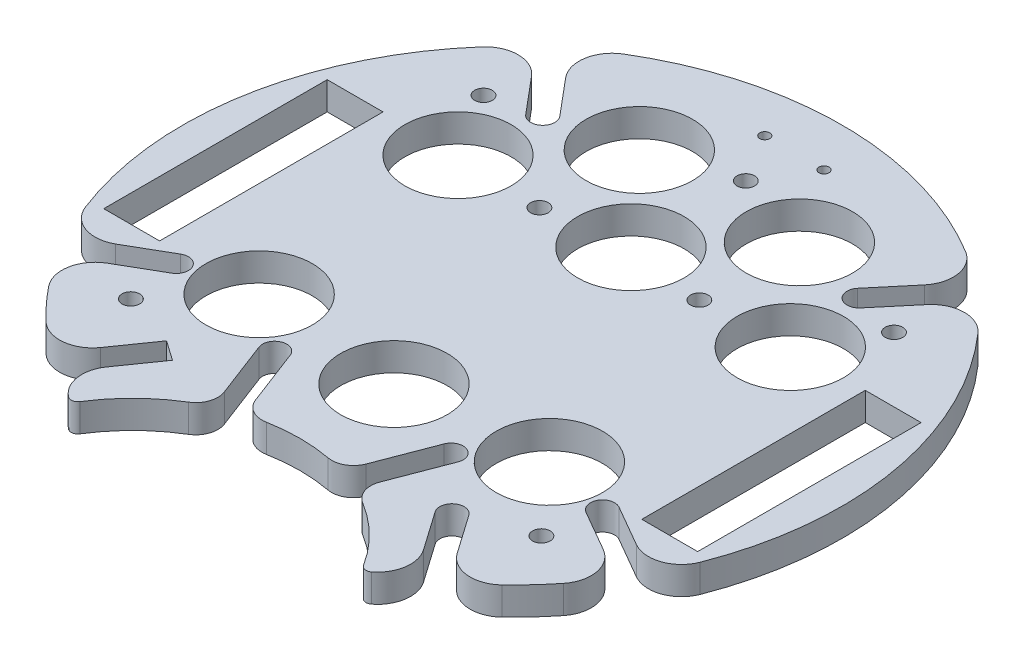
SolidWorks part; units mm, degrees
ref_plane "Front Plane" through (0, 0, 0) normal (0, 0, 1) x (1, 0, 0)
ref_plane "Top Plane" through (0, 0, 0) normal (0, 1, 0) x (1, 0, 0)
ref_plane "Right Plane" through (0, 0, 0) normal (1, 0, 0) x (0, 0, -1)
sketch "Sketch1" plane through (0, 0, 0) normal (0, 1, 0) x (1, 0, 0)
  line L0 (0, 0) -> (-32.9956, -67.352) construction
  line L1 (0, 86.2583) -> (0, -96.8543) construction
  line L2 (0, 0) -> (32.9956, -67.352) construction
  line L3 (-32.9956, -67.352) -> (0, -86.402) construction
  line L4 (32.9956, -67.352) -> (0, -86.402) construction
  line L5 (0, 0) -> (-13.6167, -50.8184) construction
  line L6 (0, 0) -> (-43.0182, -61.4364) construction
  line L7 (0, 0) -> (-48.2091, 57.4533) construction
  line L8 (-83.3992, 0) -> (107.0959, 0) construction
  line L9 (54.8141, -25.4) -> (54.8141, 25.4)
  line L10 (-67.5141, -25.4) -> (-54.8141, -25.4)
  line L11 (-67.5141, -25.4) -> (-67.5141, 25.4)
  line L12 (-67.5141, 25.4) -> (-54.8141, 25.4)
  line L13 (-54.8141, 25.4) -> (-54.8141, -25.4)
  line L14 (67.5141, 25.4) -> (54.8141, 25.4)
  line L15 (67.5141, -25.4) -> (67.5141, 25.4)
  line L16 (67.5141, -25.4) -> (54.8141, -25.4)
  line L17 (0, 0) -> (13.6167, -50.8184) construction
  line L18 (-64.9519, -37.5) -> (0, 0) construction
  line L19 (0, 0) -> (48.2091, 57.4533) construction
  line L20 (0, 0) -> (43.0182, -61.4364) construction
  line L21 (64.9519, -37.5) -> (0, 0) construction
  line L22 (-40.1627, -62.1527) -> (-39.9022, -61.7807)
  line L23 (-34.3581, -44.2739) -> (-40.5201, -53.0742)
  line L24 (44.9916, 49.3407) -> (38.0699, 41.0917)
  line L26 (-29.8527, -47.4286) -> (-36.0148, -56.2289)
  line L27 (-59.208, -31.0083) -> (-49.8282, -25.5929)
  line L30 (-44.668, -58.998) -> (-44.6824, -59.0187)
  line L31 (-56.458, -35.7715) -> (-47.0782, -30.356)
  line L32 (-40.7784, 52.876) -> (-33.8566, 44.627)
  line L34 (40.7784, 52.876) -> (33.8566, 44.627)
  line L35 (56.458, -35.7715) -> (47.0782, -30.356)
  line L36 (-44.9916, 49.3407) -> (-38.0699, 41.0917)
  line L37 (59.208, -31.0083) -> (49.8282, -25.5929)
  line L40 (34.3581, -44.2739) -> (40.5201, -53.0742)
  line L41 (29.8527, -47.4286) -> (36.0148, -56.2289)
  line L42 (-13.6167, -50.8184) -> (-2.8571, -46.701) construction
  line L43 (17.721, -47.7876) -> (22.6182, -34.9901)
  line L44 (-12.4041, -46.2927) -> (-17.4815, -33.0244)
  line L45 (-13.6167, -50.8184) -> (-17.7255, -40.0812) construction
  line L46 (-17.721, -47.7876) -> (-22.6182, -34.9901)
  line L49 (12.4041, -46.2927) -> (17.4815, -33.0244)
  line L50 (-34.3581, -44.2739) -> (-29.8527, -47.4286)
  line L51 (-49.8282, -25.5929) -> (-47.0782, -30.356)
  line L52 (-22.6182, -34.9901) -> (-17.4815, -33.0244)
  line L53 (17.4815, -33.0244) -> (22.6182, -34.9901)
  line L54 (34.3581, -44.2739) -> (29.8527, -47.4286)
  line L55 (49.8282, -25.5929) -> (47.0782, -30.356)
  line L56 (33.8566, 44.627) -> (38.0699, 41.0917)
  line L57 (-38.0699, 41.0917) -> (-33.8566, 44.627)
  arc A0 (-56.3744, 49.4664) -> (-69.893, -27.2023) centre (0, 0) ccw
  arc A1 (-19.7932, -53.8469) -> (-32.2407, -66.1006) centre (0, -86.402) ccw
  arc A2 (38.9256, 64.1077) -> (-38.9256, 64.1077) centre (0, 0) ccw
  arc A3 (56.3744, 49.4664) -> (44.9543, 49.2959) centre (50.737, 44.5198) ccw
  arc A4 (-56.3744, 49.4664) -> (-44.9543, 49.2959) centre (-50.737, 44.5198) cw
  arc A5 (-69.893, -27.2023) -> (-59.0997, -30.9458) centre (-62.9037, -24.4821) ccw
  arc A6 (-51.8486, -54.1915) -> (-40.5201, -53.0742) centre (-46.6637, -48.7724) ccw
  arc A7 (-38.9256, 64.1077) -> (-40.7407, 52.8315) centre (-35.033, 57.6969) ccw
  arc A8 (-58.5044, -46.928) -> (-56.3497, -35.7089) centre (-52.654, -42.2352) cw
  arc A9 (-34.4197, -66.4939) -> (-36.0148, -56.2289) centre (-29.8711, -60.5307) cw
  arc A10 (38.9256, 64.1077) -> (40.7407, 52.8315) centre (35.033, 57.6969) cw
  arc A11 (58.5044, -46.928) -> (56.3497, -35.7089) centre (52.654, -42.2352) ccw
  arc A12 (69.893, -27.2023) -> (59.0997, -30.9458) centre (62.9037, -24.4821) cw
  arc A13 (34.4197, -66.4939) -> (36.0148, -56.2289) centre (29.8711, -60.5307) ccw
  arc A14 (51.8486, -54.1915) -> (40.5201, -53.0742) centre (46.6637, -48.7724) cw
  arc A15 (-58.5044, -46.928) -> (-51.8486, -54.1915) centre (0, 0) ccw
  arc A16 (-33.1901, -67.2563) -> (-32.9956, -67.352) centre (0, 0) ccw
  arc A17 (51.8486, -54.1915) -> (58.5044, -46.928) centre (0, 0) ccw
  arc A18 (69.893, -27.2023) -> (56.3744, 49.4664) centre (0, 0) ccw
  arc A19 (-19.7932, -53.8469) -> (-17.721, -47.7876) centre (-22.3908, -49.5745) ccw
  arc A20 (-6.9964, -48.9499) -> (-12.5843, -45.8219) centre (-7.9145, -44.0349) cw
  arc A21 (19.7932, -53.8469) -> (17.721, -47.7876) centre (22.3908, -49.5745) cw
  arc A22 (6.9964, -48.9499) -> (12.5843, -45.8219) centre (7.9145, -44.0349) ccw
  arc A23 (6.9964, -48.9499) -> (-6.9964, -48.9499) centre (0, -86.402) ccw
  arc A24 (32.2407, -66.1006) -> (19.7932, -53.8469) centre (0, -86.402) ccw
  circle A25 centre (-18.179, 24.3106) radius 2
  circle A26 centre (-32.9956, -24.5929) radius 12.095
  circle A27 centre (32.9956, -24.5929) radius 12.095
  circle A28 centre (37.7724, 25.4) radius 12.095
  circle A29 centre (-37.7724, 25.4) radius 12.075
  circle A30 centre (-18.1963, 47.0458) radius 12.095
  circle A31 centre (18.1963, 47.0458) radius 12.095
  circle A33 centre (0, 26.9383) radius 12.095
  circle A35 centre (0, -26.9383) radius 12.095
  circle A38 centre (-46.6637, -40.0812) radius 2
  circle A39 centre (46.6637, -40.0812) radius 2
  circle A40 centre (46.6637, 40.0812) radius 2
  circle A41 centre (-46.6637, 40.0812) radius 2
  arc A42 (-34.4197, -66.4939) -> (-32.2407, -66.1006) centre (-33.51, -65.3013) ccw
  arc A43 (34.4197, -66.4939) -> (32.2407, -66.1006) centre (33.51, -65.3013) cw
  circle A44 centre (-6.731, 64.1077) radius 1.143
  circle A45 centre (6.731, 64.1077) radius 1.143
  circle A47 centre (18.179, 24.3106) radius 2
  circle A48 centre (0, 53.0612) radius 2
  point P14 (-62.6039, 0)
  point P23 (62.6039, 0)
  point P35 (-31.5178, -45.012)
  point P40 (-46.7211, -26.9744)
  point P45 (-34.6777, 41.3272)
  point P122 (-29.8711, 0)
  dimension "D1" = 150
  dimension "D3" = 120
  dimension "D2" = 76.2
  dimension "D10" = 5.5
  dimension "D15" = 13.462
  dimension "D18" = 2.286
  dimension "D12" = 4
  dimension "D4" = 50.8
  dimension "D5" = 12.7
  dimension "D6" = 80
  dimension "D7" = 80
  dimension "D8" = 25
  dimension "D9" = 30
extrude "Boss-Extrude1" add sketch "Sketch1" along normal blind 6.35
sketch "Sketch2" plane through (0, 0, 0) normal (0, 1, 0) x (1, 0, 0)
  circle A0 centre (0, 0) radius 69
  circle A1 centre (0, 0) radius 86.626
extrude "Cut-Extrude2" [suppressed] cut sketch "Sketch2" along normal blind 10
sketch "Sketch3" plane through (0, 0, 0) normal (0, 1, 0) x (1, 0, 0)
  line L1 (-74.3764, 20.7647) -> (-60.0533, 20.7647)
  line L2 (-74.3764, 20.7647) -> (-74.3764, -19.7885)
  line L3 (-74.3764, -19.7885) -> (-60.0533, -19.7885)
  line L4 (-60.0533, 20.7647) -> (-60.0533, -19.7885)
  line L5 (61.6064, 22.3178) -> (76.4472, 22.3178)
  line L6 (61.6064, 22.3178) -> (61.6064, -19.7885)
  line L7 (61.6064, -19.7885) -> (76.4472, -19.7885)
  line L8 (76.4472, 22.3178) -> (76.4472, -19.7885)
extrude "Cut-Extrude3" [suppressed] cut sketch "Sketch3" along normal blind 10
fillet "Fillet1" [suppressed] radius 5
sketch "Sketch4" [suppressed] plane through (0, 0, 0) normal (0, 1, 0) x (1, 0, 0)
  line L0 (-74.8974, 0) -> (74.8974, 0) construction
  line L1 (0, 43.1548) -> (0, -43.1548) construction
  line L2 (-54.8141, 0) -> (57.1813, 0) construction
  line L3 (-54.8141, 25.4) -> (-54.8141, -25.4) construction
  line L5 (0, 69) -> (0, -9.8243) construction
  circle A0 centre (-47.7457, 11.205) radius 1.5
  circle A1 centre (-47.7457, -11.205) radius 1.5
  circle A2 centre (-15.9457, 11.205) radius 1.5
  circle A3 centre (-15.9457, -11.205) radius 1.5
  circle A4 centre (15.9457, -11.205) radius 1.5
  circle A5 centre (15.9457, 11.205) radius 1.5
  circle A6 centre (47.7457, -11.205) radius 1.5
  circle A7 centre (47.7457, 11.205) radius 1.5
  arc A8 (41.9454, 54.7867) -> (-41.9454, 54.7867) centre (0, 0) ccw construction
  dimension "D1" = 3
  dimension "D2" = 3
  dimension "D3" = 31.8
  dimension "D4" = 22.41
extrude "Cut-Extrude4" [suppressed] cut sketch "Sketch4" along normal blind 10
sketch "Sketch5" plane through (0, 6.35, 0) normal (0, 1, 0) x (1, 0, 0)
  line L0 (-49.8282, -25.5929) -> (-47.0782, -30.356) construction
  line L1 (-22.6182, -34.9901) -> (-17.4815, -33.0244) construction
  line L2 (17.4815, -33.0244) -> (22.6182, -34.9901) construction
  line L3 (34.3581, -44.2739) -> (29.8527, -47.4286) construction
  line L4 (49.8282, -25.5929) -> (47.0782, -30.356) construction
  line L5 (33.8566, 44.627) -> (38.0699, 41.0917) construction
  line L6 (-38.0699, 41.0917) -> (-33.8566, 44.627) construction
  circle A0 centre (-48.4532, -27.9744) radius 2.75
  circle A1 centre (-20.0499, -34.0072) radius 2.75
  circle A2 centre (20.0499, -34.0072) radius 2.75
  circle A3 centre (32.1054, -45.8513) radius 2.75
  circle A4 centre (48.4532, -27.9744) radius 2.75
  circle A5 centre (35.9632, 42.8593) radius 2.75
  circle A6 centre (-35.9632, 42.8593) radius 2.75
extrude "Cut-Extrude5" cut sketch "Sketch5" against normal blind 10
